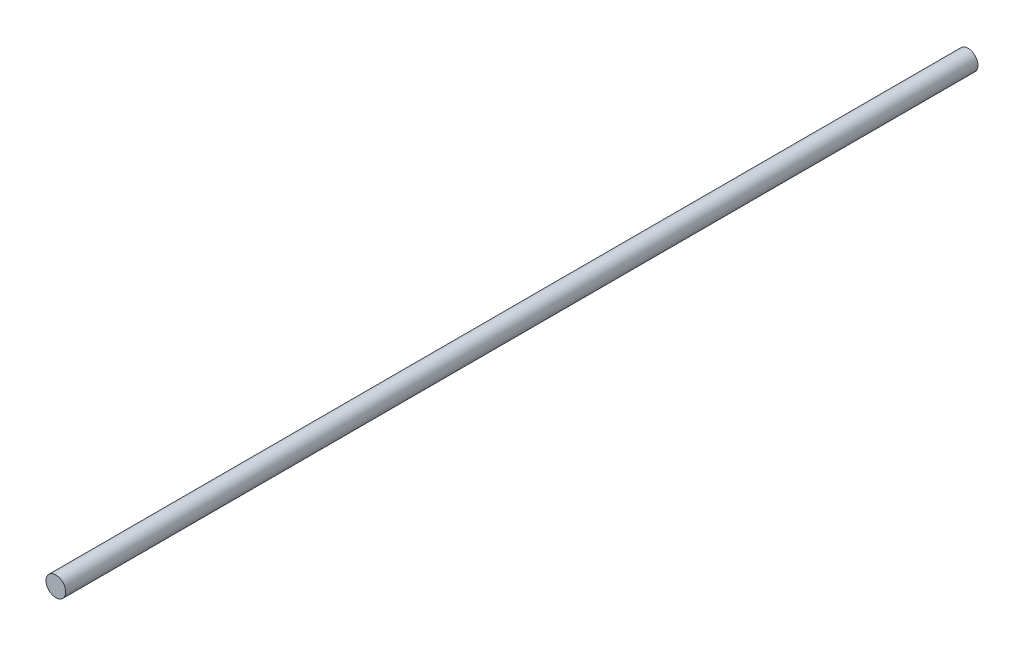
SolidWorks part; units mm, degrees
ref_plane "Front" through (0, 0, 0) normal (0, 0, 1) x (1, 0, 0)
ref_plane "Top" through (0, 0, 0) normal (0, 1, 0) x (1, 0, 0)
ref_plane "Right" through (0, 0, 0) normal (1, 0, 0) x (0, 0, -1)
sketch "Sketch1" plane through (0, 0, 0) normal (0, 0, 1) x (1, 0, 0)
  circle A0 centre (0, 0) radius 4
  dimension "D1" = 8
extrude "Boss-Extrude1" add sketch "Sketch1" along normal blind 369.52
equation "\"baseplate-height\" = 360mm"
equation "\"material-thickness\" = 9mm"
equation "\"linear-thread-dia\" = 8mm ' Diameter of the metal threaded rod used on the X Axis"
equation "\"nut_depth\"= 4.76mm"
equation "\"stepper_clearance\" = 29mm"
equation "\"rod_length_xaxis\"= \"baseplate-height\" - ( \"material-thickness\" + 20 ) + ( \"nut_depth\" * 2 ) + \"stepper_clearance\""
equation "\"D1@Boss-Extrude1\"= \"rod_length_xaxis\""
equation "\"D1@Sketch1\"=\"linear-thread-dia\""
